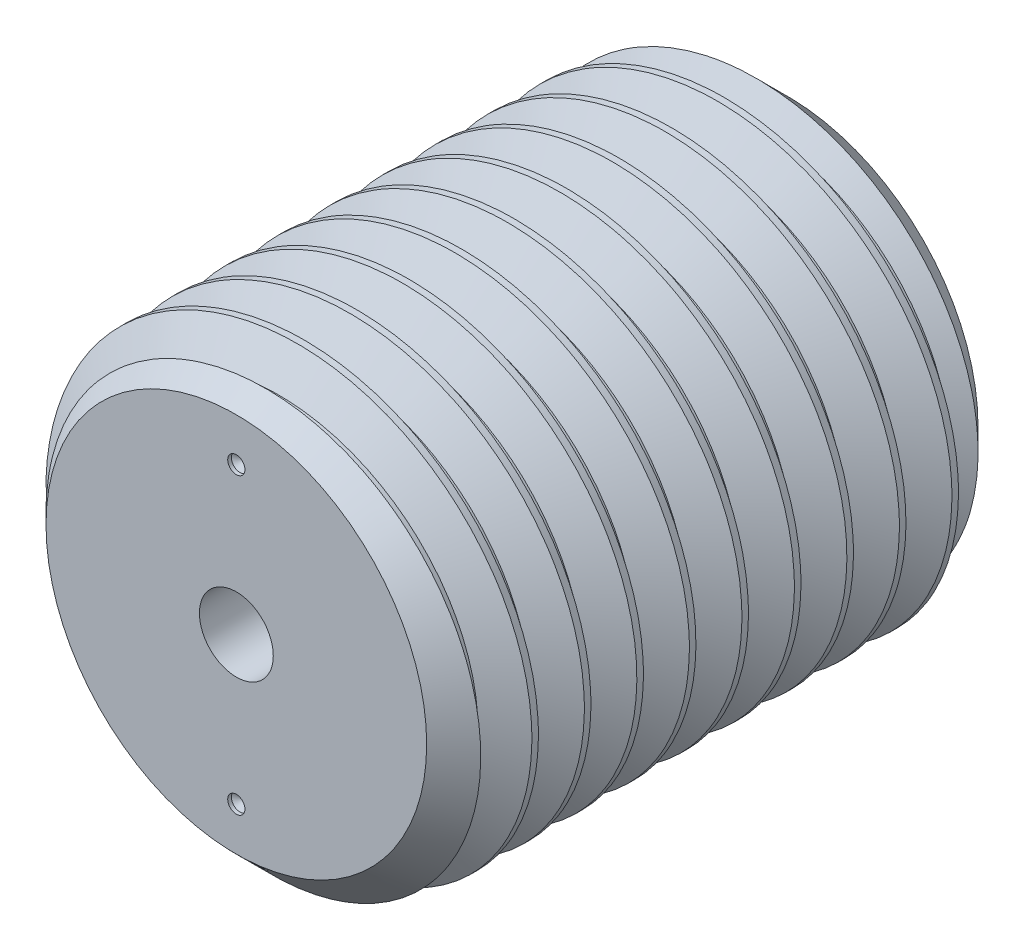
SolidWorks part; units mm, degrees
ref_plane "Front Plane" through (0, 0, 0) normal (0, 0, 1) x (1, 0, 0)
ref_plane "Top Plane" through (0, 0, 0) normal (0, 1, 0) x (1, 0, 0)
ref_plane "Right Plane" through (0, 0, 0) normal (1, 0, 0) x (0, 0, -1)
sketch "Sketch1" plane through (0, 0, 0) normal (0, 0, 1) x (1, 0, 0)
  circle A0 centre (0, 0) radius 15.875
  dimension "Diameter" = 31.75
extrude "Boss-Extrude1" add sketch "Sketch1" along normal mid plane 38.1
chamfer "Chamfer1" distance 2.7214 angle 45 2 edges at (15.875, 0, -19.05) (15.875, 0, 19.05)
sketch "Sketch4" plane through (0, 0, 19.05) normal (0, 0, 1) x (1, 0, 0)
  circle A1 centre (0, 0) radius 15.875
  circle A2 centre (0, 0) radius 15.875
  dimension "D1" = 0
curve "Helix/Spiral1" pitch 3.6286 height 41.7286 turns 11.5 parameters "Pitch"=3.6286
sketch "Sketch5" plane through (0, 0, 0) normal (1, 0, 0) x (0, 0, -1)
  line L0 (-20.8643, 13.5182) -> (-20.4107, 13.5182)
  line L1 (-20.4107, 13.5182) -> (-19.05, 15.875) construction
  line L2 (-19.05, 15.875) -> (-22.225, 15.875) construction
  line L3 (-22.225, 15.875) -> (-20.8643, 13.5182) construction
  line L4 (-20.6375, 13.5182) -> (-20.6375, 15.875) construction
  line L5 (-19.05, 15.875) -> (-19.05, -15.875) construction
  line L6 (-19.7304, 14.6966) -> (-21.5446, 14.6966) construction
  line L7 (-22.225, 15.875) -> (-22.3716, 16.129) construction
  line L8 (-22.3716, 16.129) -> (-18.9034, 16.129)
  line L9 (-18.9034, 16.129) -> (-19.05, 15.875) construction
  line L10 (-22.3716, 16.129) -> (-20.8643, 13.5182)
  line L11 (-20.4107, 13.5182) -> (-18.9034, 16.129)
  dimension "D1" = 60
  dimension "D3" = 1.8143
  dimension "D4" = 0.254
sweep "Cut-Sweep1" cut profiles "Sketch5" path "Helix/Spiral1"
sketch "Sketch6" plane through (0, 0, 0) normal (1, 0, 0) x (0, 0, -1)
  line L0 (-19.05, 0) -> (19.05, 0) construction
  line L1 (-19.05, 15.875) -> (19.05, 15.875)
  line L2 (-19.05, 15.875) -> (-19.05, -15.875)
  line L3 (-19.05, -15.875) -> (19.05, -15.875)
  line L4 (19.05, 15.875) -> (19.05, -15.875)
  point P4 (2.7214, -15.875)
  point P5 (-2.7214, -15.875)
  dimension "D1" = 38.1
  dimension "D2" = 31.75
  dimension "D3" = 16.3286
  dimension "D4" = 16.3286
hole_wizard "1/4-20 Tapped Hole1" positions "Sketch8" profile "Sketch7" tap size "1/4-20" standard "ANSI Inch"
sketch "Sketch8" plane through (0, 0, 19.05) normal (0, 0, 1) x (1, 0, 0)
  point P0 (0, 0)
sketch "Sketch7" plane through (0, 0, 19.05) normal (1, 0, 0) x (0, -1, 0)
  line L0 (0, 0) -> (0, 13.4718)
  line L1 (0, 13.4718) -> (2.5527, 11.938)
  line L2 (2.5527, 11.938) -> (2.5527, 0)
  line L5 (2.5527, 0) -> (0, 0)
  line L10 (0, 13.4718) -> (-2.5527, 11.938) construction
  line L11 (0, -6.35) -> (0, 107.95) construction
  dimension "Tap Drill Dia." = 5.1054
  dimension "Tap Drill Depth" = 11.938
  dimension "Drill Angle" = 118
cosmetic thread "Hole Thread1" parameters "D1"=8.128, "D2"=6.35
sketch "Sketch9" plane through (0, 0, 19.05) normal (0, 0, 1) x (1, 0, 0)
  line L0 (0, 13.1536) -> (0, -13.1536) construction
  circle A0 centre (0, 0) radius 13.1536 construction
hole_wizard "3/64 (0.04688) Diameter Hole1" positions "Sketch11" profile "Sketch10" hole size "3/64" standard "ANSI Inch"
sketch "Sketch11" plane through (0, 0, 19.05) normal (0, 0, 1) x (1, 0, 0)
  line L0 (0, 13.1536) -> (0, -13.1536) construction
  point P0 (0, 10.16)
  point P4 (0, -10.16)
  dimension "D1" = 10.16
  dimension "D2" = 10.16
sketch "Sketch10" plane through (0, 10.16, 19.05) normal (1, 0, 0) x (0, -1, 0)
  line L0 (0, 0) -> (0, 0.6117)
  line L1 (0, 0.6117) -> (0.5954, 0.254)
  line L2 (0.5954, 0.254) -> (0.5954, 0)
  line L5 (0.5954, 0) -> (0, 0)
  line L10 (0, 0.6117) -> (-0.5954, 0.254) construction
  line L11 (0, -6.35) -> (0, 107.95) construction
  dimension "Hole Dia." = 1.1908
  dimension "Hole Depth" = 0.254
  dimension "Drill Angle" = 118
equation "\"D2@Sketch5\" = \"Pitch@Helix/Spiral1\"*.125"
equation "\"D3@Sketch5\" = \"Pitch@Helix/Spiral1\"*.5"
equation "\"D1@Chamfer1\" = \"Pitch@Helix/Spiral1\"*.75"
equation "\"D3@Helix/Spiral1\" = \"Length@Boss-Extrude1\"+\"Pitch@Helix/Spiral1\""
equation "\"D1@Sketch6\" = \"Length@Boss-Extrude1\""
equation "\"D2@Sketch6\" = \"Diameter@Sketch1\""
equation "\"D3@Sketch6\" = \"Pitch@Helix/Spiral1\"*4.5"
equation "\"D4@Sketch6\" = \"D3@Sketch6\""
